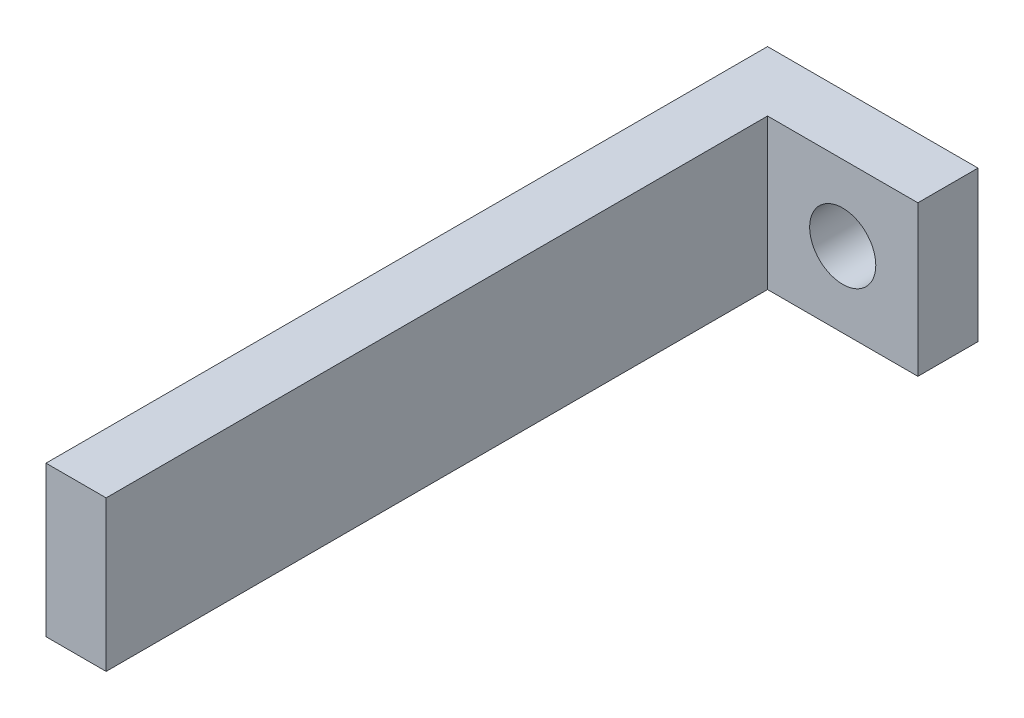
SolidWorks part; units mm, degrees
ref_plane "正面" through (0, 0, 0) normal (0, 0, 1) x (1, 0, 0)
ref_plane "平面" through (0, 0, 0) normal (0, 1, 0) x (1, 0, 0)
ref_plane "右側面" through (0, 0, 0) normal (1, 0, 0) x (0, 0, -1)
sketch "ｽｹｯﾁ1" plane through (0, 0, 0) normal (0, 0, 1) x (1, 0, 0)
  line L1 (-38.8056, 35.4193) -> (-13.8056, 35.4193)
  line L2 (-38.8056, 35.4193) -> (-38.8056, 10.4193)
  line L3 (-38.8056, 10.4193) -> (-13.8056, 10.4193)
  line L4 (-13.8056, 35.4193) -> (-13.8056, 10.4193)
  line L5 (-38.8056, 35.4193) -> (-13.8056, 10.4193) construction
  line L6 (-38.8056, 10.4193) -> (-13.8056, 35.4193) construction
  point P0 (-26.3056, 22.9193)
  dimension "D1" = 25
  dimension "D2" = 25
extrude "ﾎﾞｽ - 押し出し1" add sketch "ｽｹｯﾁ1" along normal blind 10
sketch "ｽｹｯﾁ2" plane through (0, 0, 0) normal (0, 0, -1) x (-1, 0, 0)
  line L0 (38.8056, 35.4193) -> (38.8056, 10.4193)
  line L1 (38.8056, 35.4193) -> (48.8056, 35.4193)
  line L2 (38.8056, 10.4193) -> (48.8056, 10.4193)
  line L3 (48.8056, 35.4193) -> (48.8056, 10.4193)
  dimension "D1" = 25
  dimension "D2" = 10
extrude "ﾎﾞｽ - 押し出し2" add sketch "ｽｹｯﾁ2" against normal blind 120
sketch "ｽｹｯﾁ6" plane through (0, 0, 0) normal (0, 0, -1) x (-1, 0, 0)
  line L0 (48.8056, 10.4193) -> (13.8056, 10.4193) construction
  line L1 (13.8056, 10.4193) -> (13.8056, 35.4193) construction
  circle A0 centre (26.3056, 22.9193) radius 5.5
  dimension "D1" = 12.5
  dimension "D2" = 12.5
extrude "ｶｯﾄ - 押し出し1" cut sketch "ｽｹｯﾁ6" against normal through all
